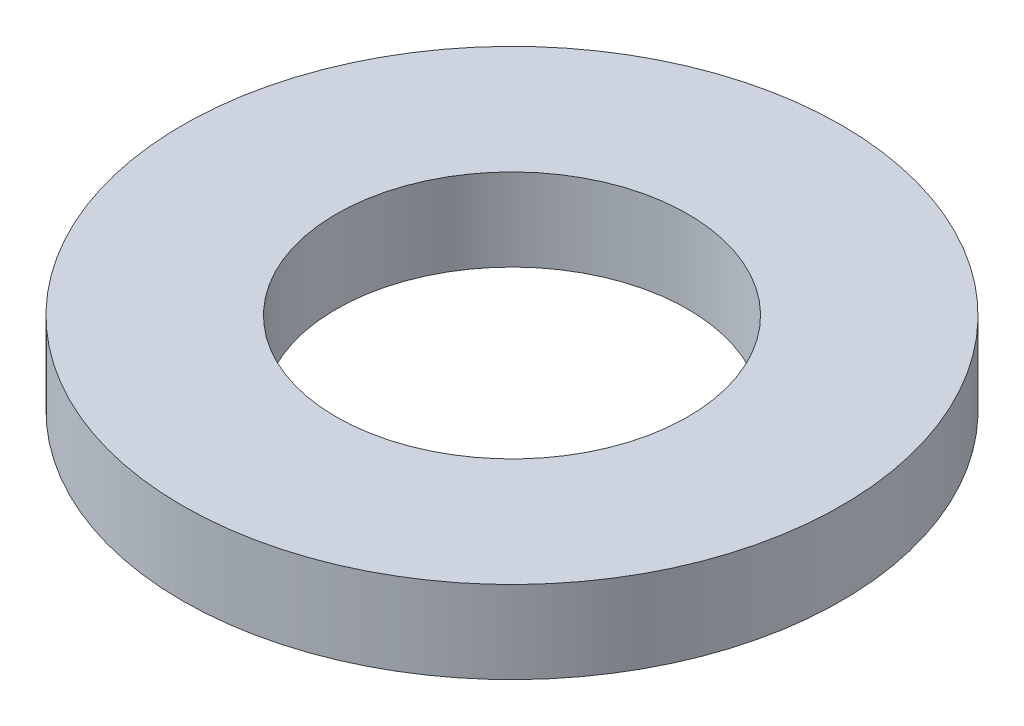
SolidWorks part; units mm, degrees
material "Nylon 101"
ref_plane "Front Plane" through (0, 0, 0) normal (0, 0, 1) x (1, 0, 0)
ref_plane "Top Plane" through (0, 0, 0) normal (0, 1, 0) x (1, 0, 0)
ref_plane "Right Plane" through (0, 0, 0) normal (1, 0, 0) x (0, 0, -1)
sketch "Sketch1" plane through (0, 0, 0) normal (0, 0, 1) x (1, 0, 0)
  line L0 (0, 0) -> (6, 0) construction
  line L1 (3.2, 0.75) -> (6, 0.75)
  line L2 (3.2, 0.75) -> (3.2, -0.75)
  line L3 (3.2, -0.75) -> (6, -0.75)
  line L4 (6, 0.75) -> (6, -0.75)
  line L5 (0, 1.4465) -> (0, -1.4465) construction
  dimension "D1" = 6.4
  dimension "D2" = 12
  dimension "D3" = 1.5
revolve "Revolve1" add sketch "Sketch1" angle 360 about L5
